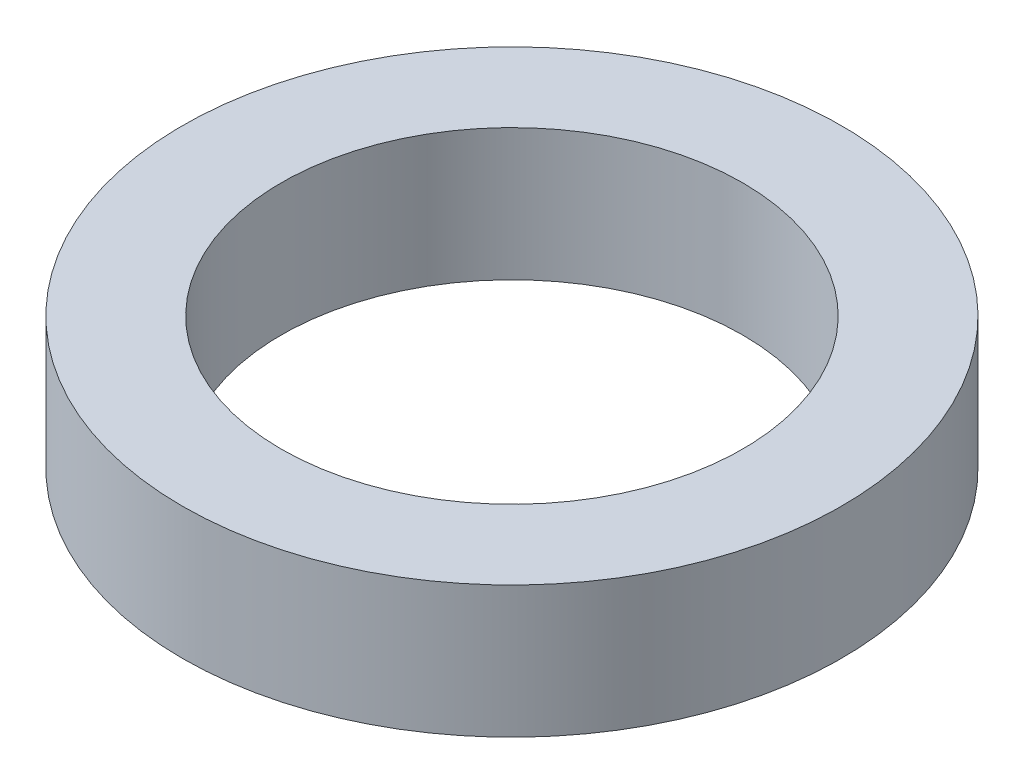
SolidWorks part; units mm, degrees
ref_plane "Front Plane" through (0, 0, 0) normal (0, 0, 1) x (1, 0, 0)
ref_plane "Top Plane" through (0, 0, 0) normal (0, 1, 0) x (1, 0, 0)
ref_plane "Right Plane" through (0, 0, 0) normal (1, 0, 0) x (0, 0, -1)
sketch "Sketch1" plane through (0, 0, 0) normal (0, 1, 0) x (1, 0, 0)
  circle A1 centre (0, 0) radius 17.5
  circle A2 centre (0, 0) radius 25
  dimension "D1" = 50
  dimension "D2" = 35
extrude "Boss-Extrude1" add sketch "Sketch1" along normal blind 10
equation "\"KeyDist\"= 15"
equation "\"ArmWidth\"= 50"
equation "\"D1@Sketch1\"=\"ArmWidth\""
